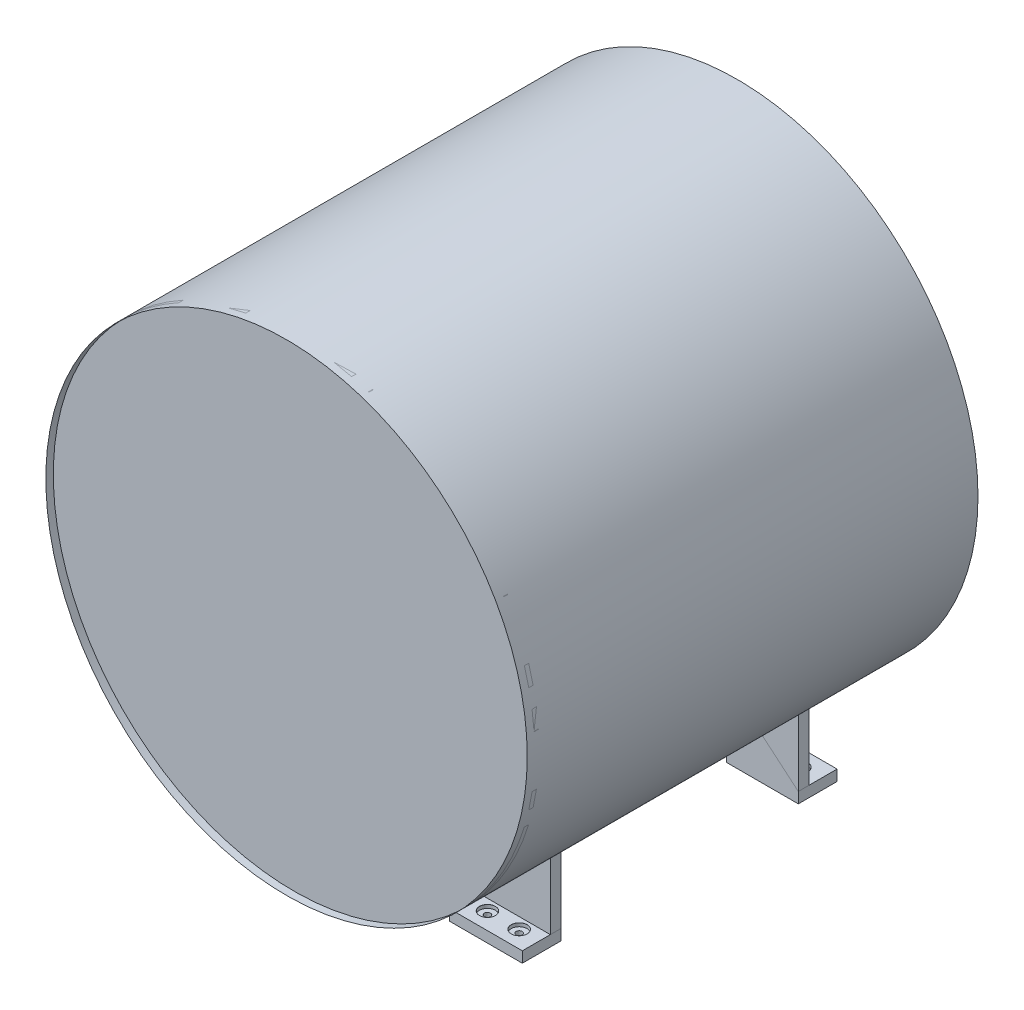
SolidWorks part; units mm, degrees
ref_plane "Front Plane" through (0, 0, 0) normal (0, 0, 1) x (1, 0, 0)
ref_plane "Top Plane" through (0, 0, 0) normal (0, 1, 0) x (1, 0, 0)
ref_plane "Right Plane" through (0, 0, 0) normal (1, 0, 0) x (0, 0, -1)
sketch "Sketch1" plane through (0, 0, 0) normal (0, 0, 1) x (1, 0, 0)
  circle A0 centre (0, 0) radius 101.5206
extrude "Boss-Extrude1" add sketch "Sketch1" along normal blind 254
sketch "Sketch2" plane through (0, 0, 0) normal (0, 1, 0) x (1, 0, 0)
  line L0 (104.48, 0) -> (104.48, -254.2165)
  line L1 (0, 0) -> (0, -254) construction
  line L2 (-101.5206, -254) -> (101.5206, -254) construction
surface "Surface-Revolve1" sketch "Sketch2" parameters "D1"=360
sketch "Sketch3" plane through (0, 0, 0) normal (0, 0, 1) x (1, 0, 0)
  circle A0 centre (0, 0) radius 137.6707
  circle A1 centre (0, 0) radius 146.4362
extrude "Boss-Extrude2" add sketch "Sketch3" along normal blind 254 contours A0
sketch "Sketch6" plane through (0, 0, 0) normal (0, 1, 0) x (1, 0, 0)
  line L0 (141.7732, 4.5512) -> (141.7732, -260.935)
  line L1 (0, 0) -> (0, -254.2165) construction
  line L2 (104.48, -254.2165) -> (-104.48, -254.2165) construction
surface "Surface-Revolve2" sketch "Sketch6" parameters "D1"=360
sketch "Sketch7" plane through (0, 0, 0) normal (0, 0, 1) x (1, 0, 0)
  circle A0 centre (0, 0) radius 141.7732
extrude "Boss-Extrude3" add sketch "Sketch7" against normal blind 2.54
sketch "Sketch8" plane through (0, 0, 254) normal (0, 0, 1) x (1, 0, 0)
  circle A0 centre (0, 0) radius 141.7732
extrude "Boss-Extrude4" add sketch "Sketch8" along normal blind 2.54
ref_plane "Plane1" through (0, 0, 50.8) normal (0, 0, 1) x (1, 0, 0)
sketch "Sketch9" plane through (0, 0, 50.8) normal (0, 0, 1) x (1, 0, 0)
  line L0 (0, -141.7732) -> (144.425, -141.7732) construction
  line L1 (97.638, -102.7933) -> (97.638, -141.7732)
  line L2 (97.638, -141.7732) -> (55.2925, -141.7732)
  line L3 (55.2925, -141.7732) -> (55.2925, -130.5465)
  line L4 (-3.9353, 171.1647) -> (3.9353, -171.1647)
  circle A0 centre (0, 0) radius 141.7732 construction
  circle A1 centre (0, 0) radius 141.7732 construction
  arc A2 (55.2925, -130.5465) -> (97.638, -102.7933) centre (0, 0) ccw
  point P14 (0, 0)
extrude "Boss-Extrude5" add sketch "Sketch9" along normal blind 6.35 separate body contours L1 L2 L3 A2
mirror "Mirror2" about plane through (0, 0, 0) normal (1, 0, 0) of bodies 108
ref_plane "Plane2" through (0, 0, 127) normal (0, 0, 1) x (1, 0, 0)
mirror "Mirror3" about plane through (0, 0, 127) normal (0, 0, 1) of bodies 109 108
sketch "Sketch11" plane through (0, -141.7732, 0) normal (0, -1, 0) x (1, 0, 0)
  line L0 (-97.638, 203.2) -> (-97.638, 219.7056)
  line L1 (-97.638, 196.85) -> (-97.638, 203.2) construction
  line L2 (-97.638, 219.7056) -> (-54.8776, 219.7056)
  line L3 (-54.8776, 219.7056) -> (-55.2925, 203.2)
  line L8 (-55.2925, 203.2) -> (-97.638, 203.2)
  line L9 (-97.638, 203.2) -> (-97.638, 196.85)
  line L10 (-97.638, 196.85) -> (-55.2925, 196.85)
  line L11 (-55.2925, 196.85) -> (-55.2925, 203.2)
  line L13 (-97.638, 203.2) -> (-97.638, 196.85)
  line L14 (-97.638, 196.85) -> (-55.2925, 196.85)
  line L15 (-55.2925, 196.85) -> (-55.2925, 203.2)
  dimension "D1" = 0
extrude "Boss-Extrude6" add sketch "Sketch11" along normal blind 6.35
mirror "Mirror4" about plane through (0, 0, 127) normal (0, 0, 1) of bodies 112
mirror "Mirror5" about plane through (0, 0, 0) normal (1, 0, 0) of bodies 112 113
hole_wizard "CBORE for M3 Hex Head Cap Screw1" positions "Sketch14" profile "Sketch13" counterbore size "M3" standard "ISO" end condition up to next
sketch "Sketch14" plane through (0, -141.7732, 0) normal (0, 1, 0) x (1, 0, 0)
  point P0 (-85.7499, -44.3481)
  point P2 (-67.0553, -44.3481)
sketch "Sketch13" plane through (-85.7499, -141.7732, 44.3481) normal (1, 0, 0) x (0, 0, 1)
  line L0 (0, 0) -> (0, 6.351)
  line L1 (0, 6.351) -> (1.8, 6.351)
  line L3 (1.8, 6.351) -> (1.8, 2)
  line L4 (4.6755, 2) -> (1.8, 2)
  line L5 (4.6755, 2) -> (4.6755, 0.025)
  line L6 (4.6755, 0.025) -> (4.7005, 0)
  line L7 (4.7005, 0) -> (0, 0)
  line L8 (-4.6755, 0.025) -> (-4.7005, 0) construction
  line L11 (0, -6.35) -> (0, 107.95) construction
  dimension "Thru Hole Dia." = 3.6
  dimension "Thru Hole Depth" = 6.351
  dimension "C'Bore Dia." = 9.351
  dimension "C'Bore Depth" = 2
  dimension "Near C'Sink Dia." = 9.401
  dimension "Near C'Sink Angle" = 90
mirror "Mirror7" about plane through (0, 0, 127) normal (0, 0, 1) of "CBORE for M3 Hex Head Cap Screw1"
mirror "Mirror8" about plane through (0, 0, 0) normal (1, 0, 0) of "CBORE for M3 Hex Head Cap Screw1", "Mirror7"
